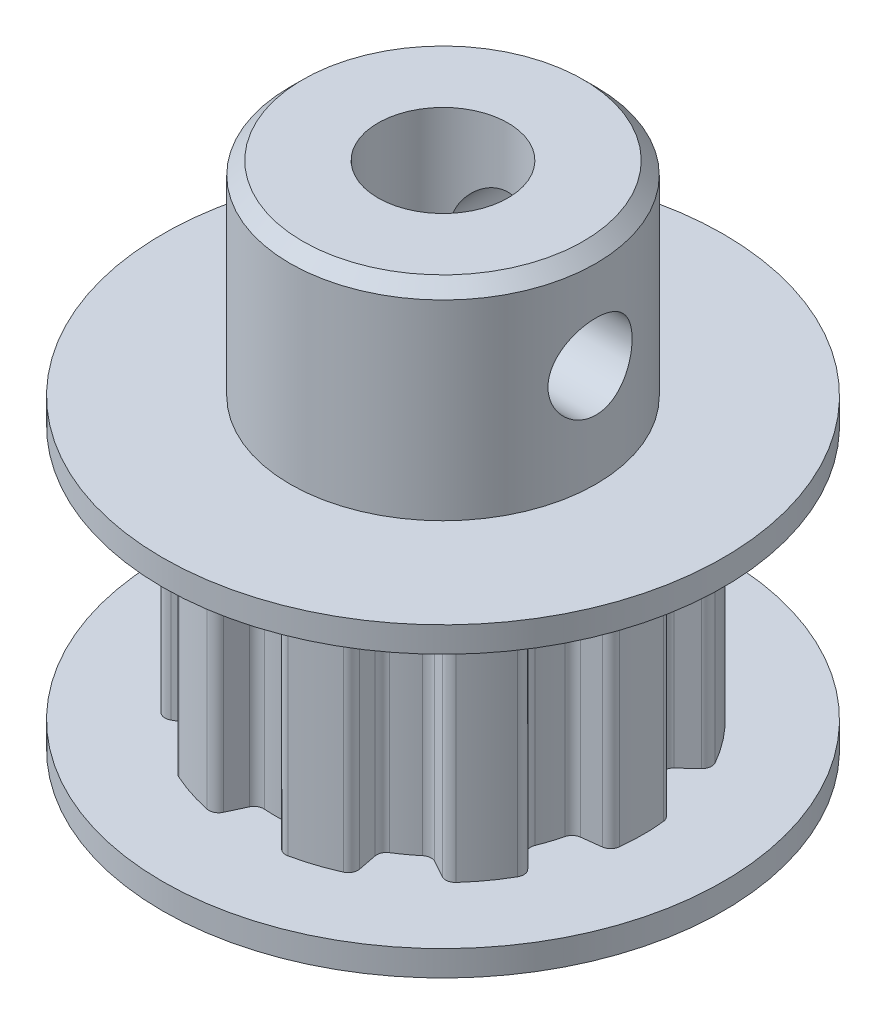
SolidWorks part; units mm, degrees
ref_plane "Front Plane" through (0, 0, 0) normal (0, 0, 1) x (1, 0, 0)
ref_plane "Top Plane" through (0, 0, 0) normal (0, 1, 0) x (1, 0, 0)
ref_plane "Right Plane" through (0, 0, 0) normal (1, 0, 0) x (0, 0, -1)
sketch "Sketch1" plane through (0, 0, 0) normal (0, 1, 0) x (1, 0, 0)
  circle A0 centre (0, 0) radius 7.83
  dimension "D1" = 15.66
extrude "Boss-Extrude1" add sketch "Sketch1" along normal blind 10
ref_plane "Plane1" through (0, 2, 0) normal (0, 1, 0) x (1, 0, 0)
sketch "Sketch2" plane through (0, 2, 0) normal (0, 1, 0) x (1, 0, 0)
  line L0 (0, 0) -> (0, 10.0333) construction
  line L1 (-1.285, 7.7238) -> (-0.7236, 6.52)
  line L2 (1.285, 7.7238) -> (0.7236, 6.52)
  line L3 (0, 6.56) -> (1.5713, 6.56) construction
  line L4 (0, 7.83) -> (0.9353, 7.83) construction
  arc A0 (-1.285, 7.7238) -> (1.285, 7.7238) centre (0, 0) cw
  circle A1 centre (0, 0) radius 7.83 construction
  arc A2 (-0.7236, 6.52) -> (0.7236, 6.52) centre (0, 0) cw
  dimension "D1" = 25
  dimension "D2" = 25
  dimension "D3" = 1.27
  dimension "D4" = 1.285
  dimension "D5" = 1.285
extrude "Cut-Extrude1" cut sketch "Sketch2" against normal through all both and the other way through all
fillet "Fillet1" radius 0.38 4 edges at (1.285, 5, -7.7238) (0.7236, 5, -6.52) (-0.7236, 5, -6.52) (-1.285, 5, -7.7238)
pattern_circular "CirPattern1" count 10 over 360 about axis through (0, 0, 0) along (0, 1, 0) of "Cut-Extrude1", "Fillet1"
sketch "Sketch3" plane through (0, 10, 0) normal (0, 1, 0) x (1, 0, 0)
  circle A0 centre (0, 0) radius 2.55
  dimension "D1" = 5.1
extrude "Cut-Extrude2" cut sketch "Sketch3" against normal through all
sketch "Sketch4" plane through (0, 0, 0) normal (0, -1, 0) x (1, 0, 0)
  circle A0 centre (0, 0) radius 11
  dimension "D1" = 22
extrude "Boss-Extrude2" add sketch "Sketch4" along normal blind 1
sketch "Sketch5" plane through (0, 10, 0) normal (0, 1, 0) x (1, 0, 0)
  circle A0 centre (0, 0) radius 11
extrude "Boss-Extrude3" add sketch "Sketch5" along normal blind 1
sketch "Sketch6" plane through (0, 11, 0) normal (0, 1, 0) x (1, 0, 0)
  circle A0 centre (0, 0) radius 6
  dimension "D1" = 12
extrude "Boss-Extrude4" add sketch "Sketch6" along normal blind 8
sketch "Sketch7" plane through (0, 19, 0) normal (0, 1, 0) x (1, 0, 0)
  circle A0 centre (0, 0) radius 2.55
  dimension "D1" = 5.1
extrude "Cut-Extrude3" cut sketch "Sketch7" against normal through all both and the other way through all
ref_plane "Plane2" through (0, 0, -6) normal (0, 0, 1) x (1, 0, 0)
ref_plane "Plane3" through (6, 0, 0) normal (1, 0, 0) x (0, 0, -1)
sketch "Sketch9" plane through (0, 0, -6) normal (0, 0, 1) x (1, 0, 0)
  line L0 (2.2763, 19) -> (9.6255, 19) construction
  line L1 (2.55, 19) -> (-2.55, 19) construction
  line L2 (0, 0) -> (13.3976, 0) construction
  line L3 (9.6255, 19) -> (9.6255, 0) construction
  line L4 (9.6255, 19) -> (9.6255, 15) construction
  dimension "D1" = 4
hole_wizard "M4 Tapped Hole1" positions "3DSketch2" profile "Sketch10" tap size "M4" standard "GB"
sketch3d "3DSketch2"
  point P0 (0, 15, -6)
sketch "Sketch10" plane through (0, 15, -6) normal (1, 0, 0) x (0, 1, 0)
  line L0 (0, 0) -> (0, 3.45)
  line L1 (0, 3.45) -> (1.65, 3.45)
  line L2 (1.65, 3.45) -> (1.65, 0)
  line L5 (1.65, 0) -> (0, 0)
  line L11 (0, -6.35) -> (0, 107.95) construction
  dimension "Thru Tap Drill Dia." = 3.3
  dimension "Thru Tap Drill Depth" = 3.45
cosmetic thread "Hole Thread1" parameters "D2"=4
hole_wizard "M4 Tapped Hole2" positions "3DSketch3" profile "Sketch11" tap size "M4" standard "GB"
sketch3d "3DSketch3"
  point P0 (6, 15, 0)
sketch "Sketch11" plane through (6, 15, 0) normal (0, 1, 0) x (0, 0, -1)
  line L0 (0, 0) -> (0, 3.45)
  line L1 (0, 3.45) -> (1.65, 3.45)
  line L2 (1.65, 3.45) -> (1.65, 0)
  line L5 (1.65, 0) -> (0, 0)
  line L11 (0, -6.35) -> (0, 107.95) construction
  dimension "Thru Tap Drill Dia." = 3.3
  dimension "Thru Tap Drill Depth" = 3.45
cosmetic thread "Hole Thread2" parameters "D2"=4
chamfer "Chamfer1" distance 0.5 angle 45 1 edges at (0, 19, 6)
sketch "Sketch12" plane through (0, 11, 0) normal (0, 1, 0) x (1, 0, 0)
  line L0 (0, 0) -> (0, 12.331) construction
  line L1 (0, 0) -> (15.5309, 0) construction
sketch "Sketch13" plane through (0, 0, 0) normal (1, 0, 0) x (0, 0, -1)
  line L0 (0, 0) -> (0, 19.5685) construction
sketch "Sketch16" plane through (0, 11, 0) normal (0, 1, 0) x (1, 0, 0)
  line L0 (0, 0) -> (0, 14.0644)
sketch "Sketch18" plane through (0, -1, 0) normal (0, -1, 0) x (1, 0, 0)
  line L0 (0, 0) -> (0, 22.964)
